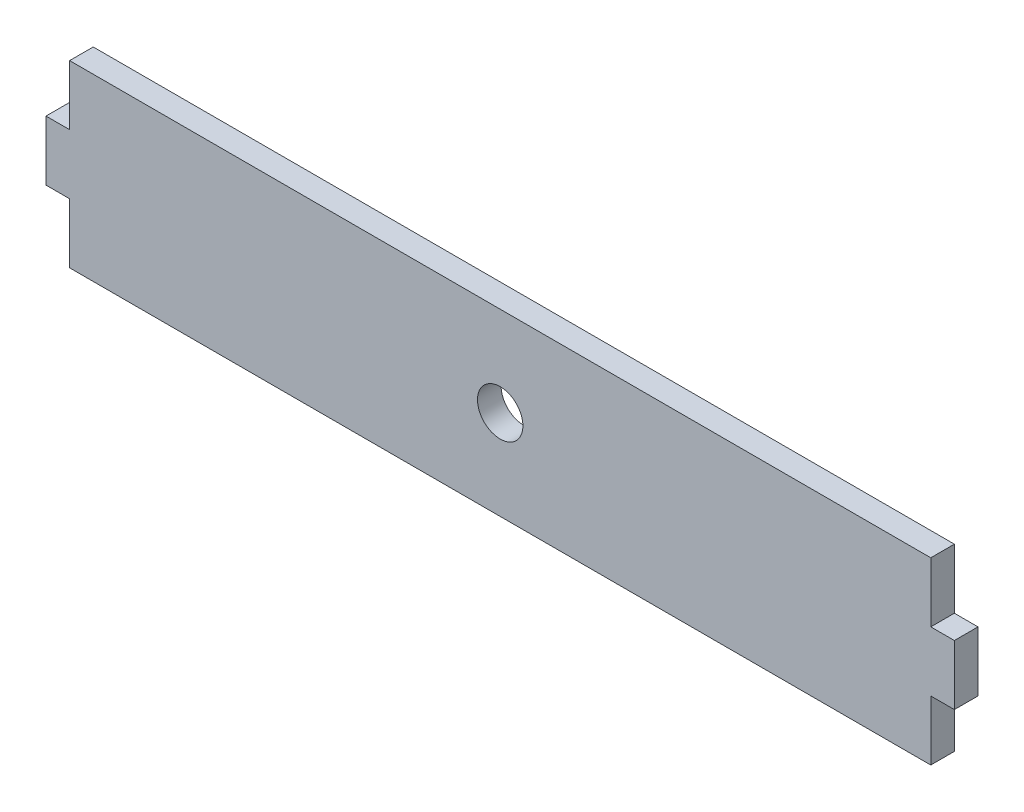
SolidWorks part; units mm, degrees
ref_plane "Front Plane" through (0, 0, 0) normal (0, 0, 1) x (1, 0, 0)
ref_plane "Top Plane" through (0, 0, 0) normal (0, 1, 0) x (1, 0, 0)
ref_plane "Right Plane" through (0, 0, 0) normal (1, 0, 0) x (0, 0, -1)
sketch "Sketch1" plane through (0, 0, 0) normal (0, 0, 1) x (1, 0, 0)
  line L0 (0, 8.718) -> (100, 8.718) construction
  line L1 (2.6, -1.1624) -> (97.4, -1.1624)
  line L2 (0, 5.4246) -> (0, 12.0115)
  line L3 (2.6, 18.5985) -> (97.4, 18.5985)
  line L4 (100, 5.4246) -> (100, 12.0115)
  line L6 (50, 18.5985) -> (50, -1.1624) construction
  line L7 (0, 12.0115) -> (2.6, 12.0115)
  line L8 (2.6, 18.5985) -> (2.6, 12.0115)
  line L11 (0, 5.4246) -> (2.6, 5.4246)
  line L12 (2.6, -1.1624) -> (2.6, 5.4246)
  line L15 (100, 12.0115) -> (97.4, 12.0115)
  line L16 (97.4, 18.5985) -> (97.4, 12.0115)
  line L19 (100, 5.4246) -> (97.4, 5.4246)
  line L20 (97.4, -1.1624) -> (97.4, 5.4246)
  circle A0 centre (50, 8.718) radius 2.5
  point P17 (50, 8.718)
  dimension "D3" = 5
  dimension "D1" = 100
  dimension "D2" = 2.6
extrude "Boss-Extrude1" add sketch "Sketch1" along normal blind 2.6
equation "\"D2@Sketch1\" = \"mdf@fmv1.assembly\""
equation "\"D1@Boss-Extrude1\"=\"mdf@fmv1.assembly\""
